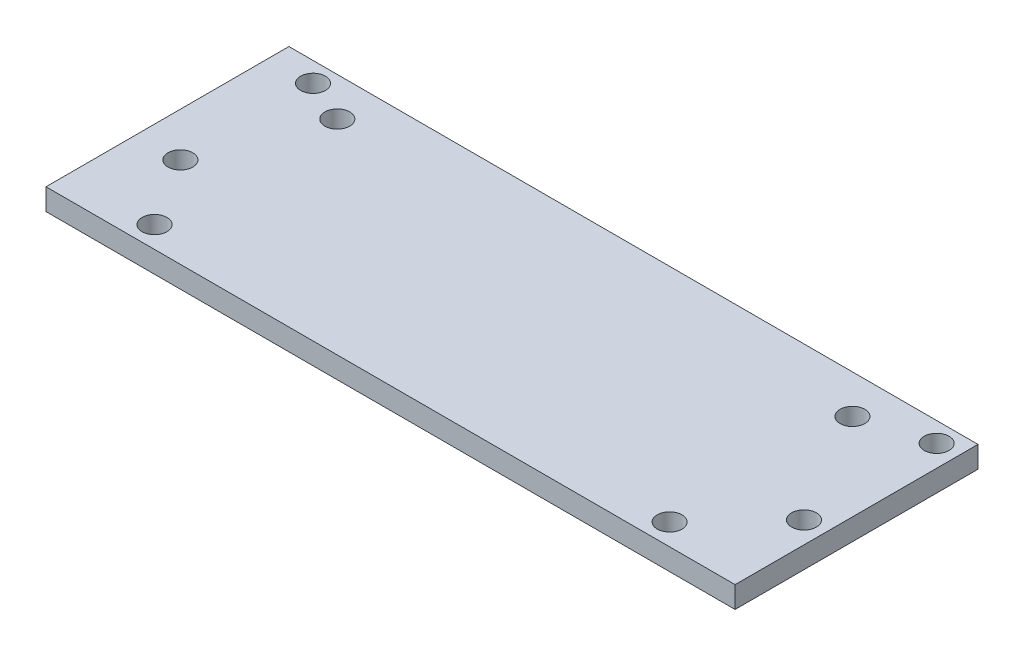
SolidWorks part; units mm, degrees
ref_plane "Front" through (0, 0, 0) normal (0, 0, 1) x (1, 0, 0)
ref_plane "Top" through (0, 0, 0) normal (0, 1, 0) x (1, 0, 0)
ref_plane "Right" through (0, 0, 0) normal (1, 0, 0) x (0, 0, -1)
sketch "Sketch2" plane through (0, 0, 0) normal (0, 1, 0) x (1, 0, 0)
  line L1 (50.8, -17.907) -> (-50.8, -17.907)
  line L2 (50.8, -17.907) -> (50.8, 17.907)
  line L3 (50.8, 17.907) -> (-50.8, 17.907)
  line L4 (-50.8, -17.907) -> (-50.8, 17.907)
  line L5 (50.8, -17.907) -> (-50.8, 17.907) construction
  line L6 (50.8, 17.907) -> (-50.8, -17.907) construction
  point P0 (0, 0)
  dimension "D1" = 101.6
  dimension "D2" = 35.814
extrude "Boss-Extrude1" add sketch "Sketch2" along normal blind 3.175
sketch "Sketch3" plane through (0, 3.175, 0) normal (0, 1, 0) x (1, 0, 0)
  line L0 (50.8, 17.907) -> (47.625, 17.907) construction
  line L1 (50.8, 17.907) -> (-50.8, 17.907) construction
  line L2 (47.625, 17.907) -> (47.625, 14.986) construction
  line L3 (47.625, 14.986) -> (47.625, -4.572) construction
  line L4 (-50.8, 17.907) -> (-47.498, 17.907) construction
  line L5 (-47.498, 17.907) -> (-47.498, -17.907) construction
  line L6 (-50.8, -17.907) -> (50.8, -17.907) construction
  line L7 (-47.498, 17.907) -> (-44.323, 17.907) construction
  line L8 (-44.323, 17.907) -> (-44.323, 14.986) construction
  line L9 (-44.323, 14.986) -> (-44.323, -4.572) construction
  circle A0 centre (47.625, 14.986) radius 1.8288
  circle A1 centre (47.625, -4.572) radius 1.8288
  circle A2 centre (-44.323, 14.986) radius 1.8288
  circle A3 centre (-44.323, -4.572) radius 1.8288
  dimension "D3" = 3.6576
  dimension "D5" = 3.6576
  dimension "D9" = 3.6576
  dimension "D10" = 3.6576
  dimension "D1" = 3.175
  dimension "D2" = 2.921
  dimension "D4" = 19.558
  dimension "D6" = 3.302
  dimension "D7" = 3.175
  dimension "D8" = 2.921
extrude "Cut-Extrude1" cut sketch "Sketch3" against normal through all
sketch "Sketch4" plane through (0, 3.175, 0) normal (0, 1, 0) x (1, 0, 0)
  line L0 (0, 17.907) -> (0, -17.907) construction
  line L1 (50.8, 17.907) -> (-50.8, 17.907) construction
  line L2 (-50.8, -17.907) -> (50.8, -17.907) construction
  line L3 (-44.323, 14.986) -> (-37.973, 14.986) construction
  line L4 (-37.973, -17.907) -> (-37.973, -14.732) construction
  line L5 (-37.973, -14.732) -> (-37.973, 12.2174) construction
  circle A0 centre (-37.973, -14.732) radius 1.8288
  circle A1 centre (-37.973, 12.2174) radius 1.8288
  circle A2 centre (37.973, -14.732) radius 1.8288
  circle A3 centre (37.973, 12.2174) radius 1.8288
  dimension "D2" = 3.175
  dimension "D4" = 26.9494
  dimension "D3" = 3.6576
  dimension "D1" = 6.35
extrude "Cut-Extrude2" cut sketch "Sketch4" against normal through all
